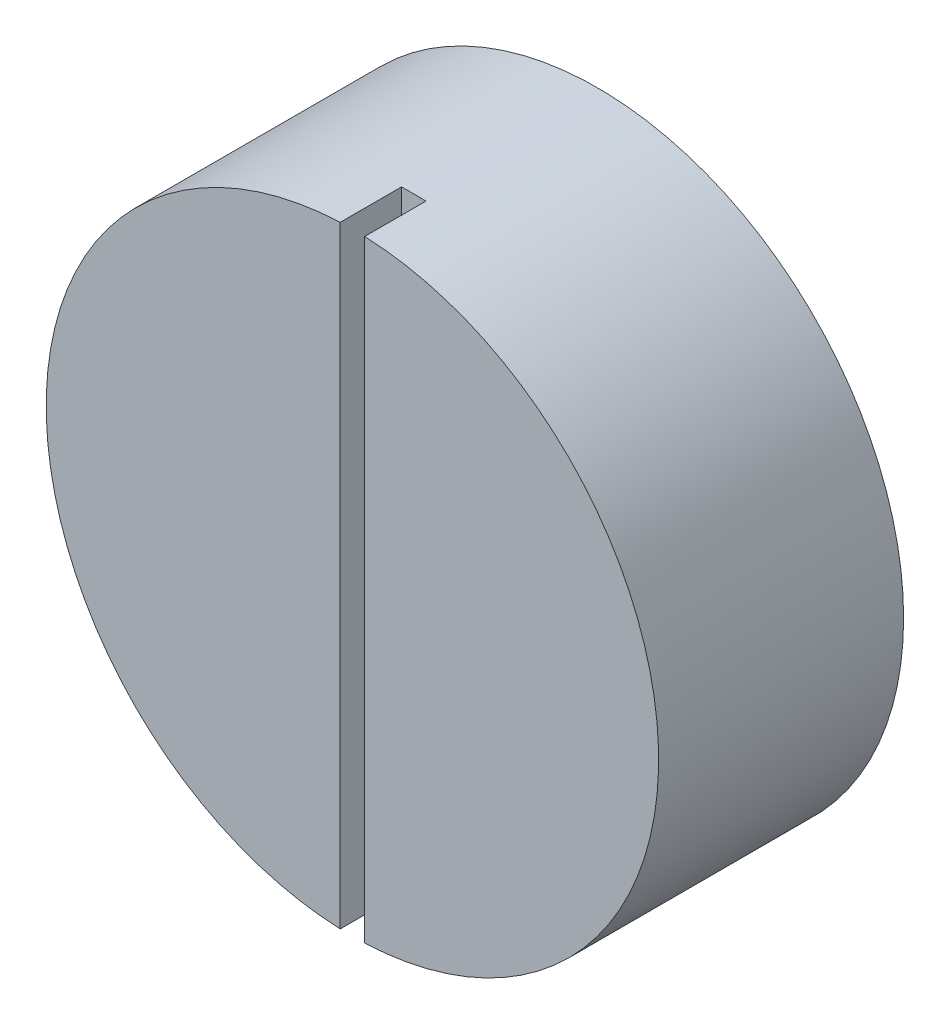
SolidWorks part; units mm, degrees
ref_plane "Front Plane" through (0, 0, 0) normal (0, 0, 1) x (1, 0, 0)
ref_plane "Top Plane" through (0, 0, 0) normal (0, 1, 0) x (1, 0, 0)
ref_plane "Right Plane" through (0, 0, 0) normal (1, 0, 0) x (0, 0, -1)
sketch "Sketch1" plane through (0, 0, 0) normal (0, 0, 1) x (1, 0, 0)
  circle A0 centre (0, 0) radius 25
  dimension "D1" = 50
extrude "Boss-Extrude1" add sketch "Sketch1" along normal blind 20
sketch "Sketch2" plane through (0, 0, 20) normal (0, 0, 1) x (1, 0, 0)
  line L1 (-1, 25) -> (1, 25)
  line L2 (-1, 25) -> (-1, -25)
  line L3 (1, -25) -> (-1, -25)
  line L4 (1, 25) -> (1, -25)
  line L5 (-1, 25) -> (1, -25) construction
  line L6 (-1, -25) -> (1, 25) construction
  point P0 (0, 0)
extrude "Cut-Extrude1" cut sketch "Sketch2" against normal blind 5
